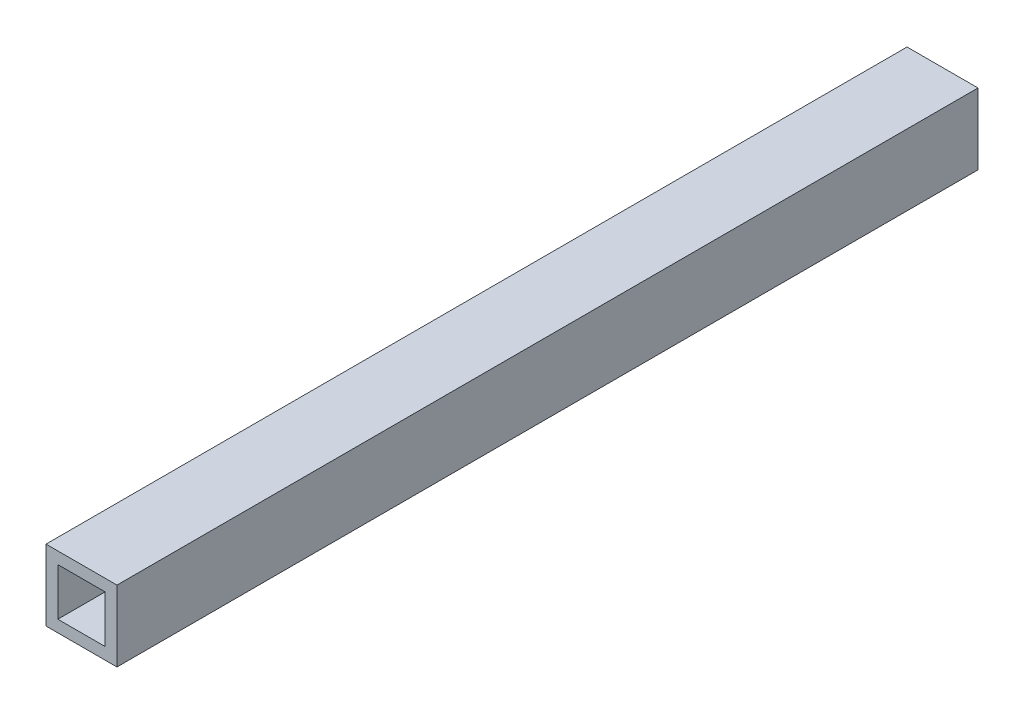
SolidWorks part; units mm, degrees
material "5052-H36"
ref_plane "Front Plane" through (0, 0, 0) normal (0, 0, 1) x (1, 0, 0)
ref_plane "Top Plane" through (0, 0, 0) normal (0, 1, 0) x (1, 0, 0)
ref_plane "Right Plane" through (0, 0, 0) normal (1, 0, 0) x (0, 0, -1)
sketch "Sketch1" plane through (0, 0, 0) normal (0, 0, 1) x (1, 0, 0)
  line L1 (9.525, -9.525) -> (-9.525, -9.525)
  line L2 (9.525, -9.525) -> (9.525, 9.525)
  line L3 (9.525, 9.525) -> (-9.525, 9.525)
  line L4 (-9.525, -9.525) -> (-9.525, 9.525)
  line L5 (9.525, -9.525) -> (-9.525, 9.525) construction
  line L6 (9.525, 9.525) -> (-9.525, -9.525) construction
  line L7 (6.35, -6.35) -> (-6.35, -6.35)
  line L8 (6.35, -6.35) -> (6.35, 6.35)
  line L9 (6.35, 6.35) -> (-6.35, 6.35)
  line L10 (-6.35, -6.35) -> (-6.35, 6.35)
  line L11 (6.35, -6.35) -> (-6.35, 6.35) construction
  line L12 (6.35, 6.35) -> (-6.35, -6.35) construction
  point P0 (0, 0)
  point P6 (0, 0)
  dimension "D1" = 19.05
  dimension "D2" = 3.175
extrude "Boss-Extrude1" add sketch "Sketch1" along normal blind 231.14
sketch "Sketch2" [suppressed] plane through (0, 9.525, 0) normal (0, 1, 0) x (1, 0, 0)
  line L0 (-9.525, -469.9) -> (9.525, -436.9044)
  line L1 (-9.525, -584.2) -> (-9.525, 0) construction
  line L2 (9.525, -584.2) -> (9.525, 0) construction
  line L3 (9.525, -436.9044) -> (9.525, 0)
  line L4 (9.525, 0) -> (-9.525, 0)
  line L5 (-9.525, 0) -> (-9.525, -469.9)
  line L10 (9.525, 0) -> (-9.525, 0)
  line L11 (-9.525, 0) -> (-9.525, -584.2)
  line L12 (-9.525, -584.2) -> (9.525, -584.2)
  line L13 (9.525, -584.2) -> (9.525, 0)
  line L14 (9.525, 0) -> (-9.525, 0)
  line L15 (-9.525, 0) -> (-9.525, -584.2)
  line L16 (-9.525, -584.2) -> (9.525, -584.2) construction
  line L17 (9.525, -584.2) -> (9.525, 0)
  dimension "D2" = 114.3
  dimension "D3" = 30
  dimension "D1" = 0
extrude "Cut-Extrude1" [suppressed] cut sketch "Sketch2" against normal blind 55.88
sketch "Sketch3" [suppressed] plane through (0, 9.525, 0) normal (0, 1, 0) x (1, 0, 0)
  line L0 (-9.525, -574.675) -> (-9.525, 0) construction
  line L1 (-9.525, -133.8485) -> (9.525, -152.8985)
  line L2 (9.525, -574.675) -> (9.525, 0) construction
  line L3 (9.525, -368.4247) -> (-9.525, -387.4747)
  line L4 (-9.525, -133.8485) -> (-9.525, 0)
  line L5 (-9.525, 0) -> (9.525, 0)
  line L6 (9.525, 0) -> (9.525, -152.8985)
  line L7 (9.525, -368.4247) -> (9.525, -574.675)
  line L8 (9.525, -574.675) -> (-9.525, -574.675)
  line L9 (-9.525, -574.675) -> (-9.525, -387.4747)
  dimension "D1" = 45
  dimension "D2" = 45
  dimension "D3" = 152.4
extrude "Cut-Extrude2" [suppressed] cut sketch "Sketch3" against normal through all
sketch "Sketch4" [suppressed] plane through (0, 9.525, 0) normal (0, 1, 0) x (1, 0, 0)
  line L0 (-9.525, -387.4747) -> (-3.9454, -381.8951)
  line L2 (-9.525, -387.4747) -> (-9.525, -376.3155)
  line L4 (-9.525, -387.4747) -> (-9.525, -133.8485) construction
  line L5 (-9.525, -133.8485) -> (-9.525, -145.0078)
  line L8 (-9.525, -133.8485) -> (9.525, -152.8985) construction
  line L9 (-9.525, -145.0078) -> (-3.9454, -139.4282)
  line L10 (-9.525, -376.3155) -> (-3.9454, -381.8951)
  line L11 (-3.9454, -139.4282) -> (-9.525, -133.8485)
  dimension "D1" = 19.05
  dimension "D2" = 19.05
extrude "Cut-Extrude3" [suppressed] cut sketch "Sketch4" against normal through all
ref_plane "Plane1" [suppressed] through (0, 0, 145.0078) normal (0, 0, 1) x (0, 1, 0)
ref_plane "Plane2" [suppressed] through (0, 0, 376.3155) normal (0, 0, 1) x (1, 0, 0)
ref_plane "Plane3" [suppressed] through (0, 0, 260.6616) normal (0, 0, 1) x (1, 0, 0)
fillet "Fillet1" [suppressed] radius 2.54
fillet "Fillet2" [suppressed] radius 6.35
fillet "Fillet3" [suppressed] radius 12.7
fillet "Fillet4" [suppressed] radius 12.7
ref_plane "Plane4" through (0, 0, 115.57) normal (0, 0, -1) x (-1, 0, 0)
